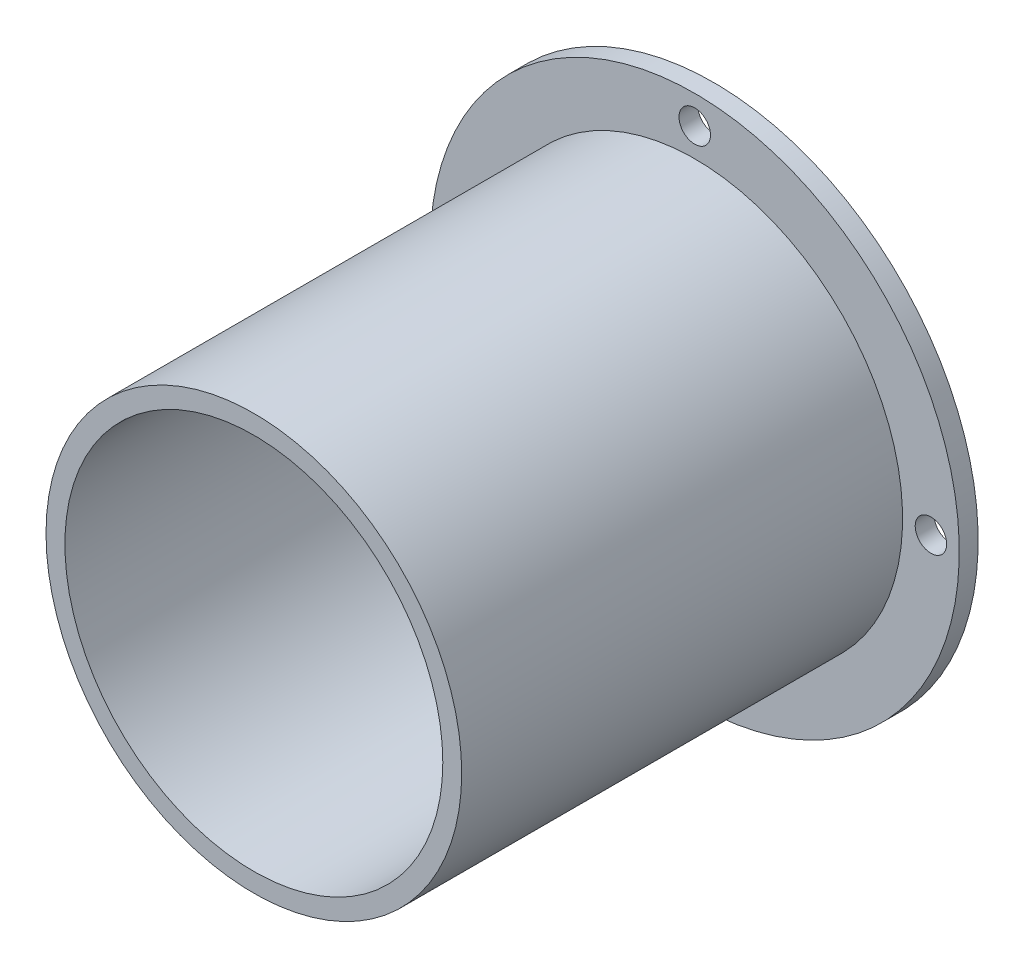
SolidWorks part; units mm, degrees
ref_plane "Front Plane" through (0, 0, 0) normal (0, 0, 1) x (1, 0, 0)
ref_plane "Top Plane" through (0, 0, 0) normal (0, 1, 0) x (1, 0, 0)
ref_plane "Right Plane" through (0, 0, 0) normal (1, 0, 0) x (0, 0, -1)
sketch "Sketch2" plane through (0, 0, 0) normal (0, 0, 1) x (1, 0, 0)
  circle A1 centre (0, 0) radius 16.5
extrude "Boss-Extrude1" add sketch "Sketch2" along normal blind 33
shell "Shell2" thickness 1.5
sketch "Sketch6" plane through (0, 0, 0) normal (0, 0, -1) x (-1, 0, 0)
  circle A0 centre (0, 0) radius 2.5
  dimension "D1" = 5
extrude "Cut-Extrude3" cut sketch "Sketch6" against normal blind 1.5
sketch "Sketch7" plane through (0, 0, 0) normal (0, 0, -1) x (-1, 0, 0)
  circle A0 centre (0, 0) radius 16.5
  circle A1 centre (0, 0) radius 15
  dimension "D1" = 1.5
extrude "Boss-Extrude3" add sketch "Sketch7" along normal blind 2
sketch "Sketch8" plane through (0, 0, -2) normal (0, 0, -1) x (-1, 0, 0)
  circle A0 centre (0, 0) radius 16.5
  circle A1 centre (0, 0) radius 21
  circle A2 centre (0, 18.75) radius 1.25
  circle A3 centre (18.75, 0) radius 1.25
  circle A4 centre (0, -18.75) radius 1.25
  circle A5 centre (-18.75, 0) radius 1.25
  point P15 (0, 0)
  dimension "D1" = 42
  dimension "D2" = 2.5
  dimension "D4" = 18.75
  dimension "D3" = 4
extrude "Boss-Extrude4" add sketch "Sketch8" along normal blind 1.5 separate body
